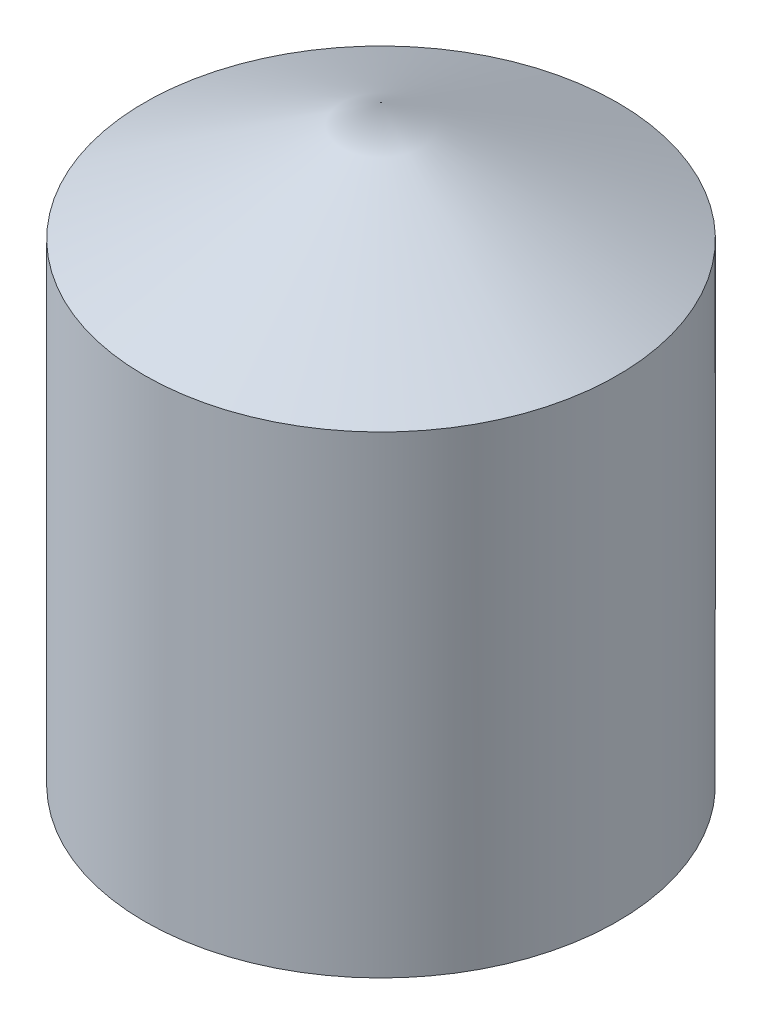
SolidWorks part; units mm, degrees
ref_plane "Front Plane" through (0, 0, 0) normal (0, 0, 1) x (1, 0, 0)
ref_plane "Top Plane" through (0, 0, 0) normal (0, 1, 0) x (1, 0, 0)
ref_plane "Right Plane" through (0, 0, 0) normal (1, 0, 0) x (0, 0, -1)
sketch "Sketch1" plane through (0, 0, 0) normal (0, 1, 0) x (1, 0, 0)
  circle A0 centre (0, 0) radius 25.4
extrude "Boss-Extrude1" add sketch "Sketch1" along normal blind 50.8
sketch "Sketch2" plane through (0, 0, 0) normal (0, 0, 1) x (1, 0, 0)
  line L0 (0, 50.8) -> (0, 63.5)
  line L1 (25.4, 50.8) -> (-25.4, 50.8) construction
  line L2 (0, 63.5) -> (25.4, 50.8)
  line L3 (25.4, 50.8) -> (0, 50.8)
revolve "Revolve1" add sketch "Sketch2" angle 360 about L0
